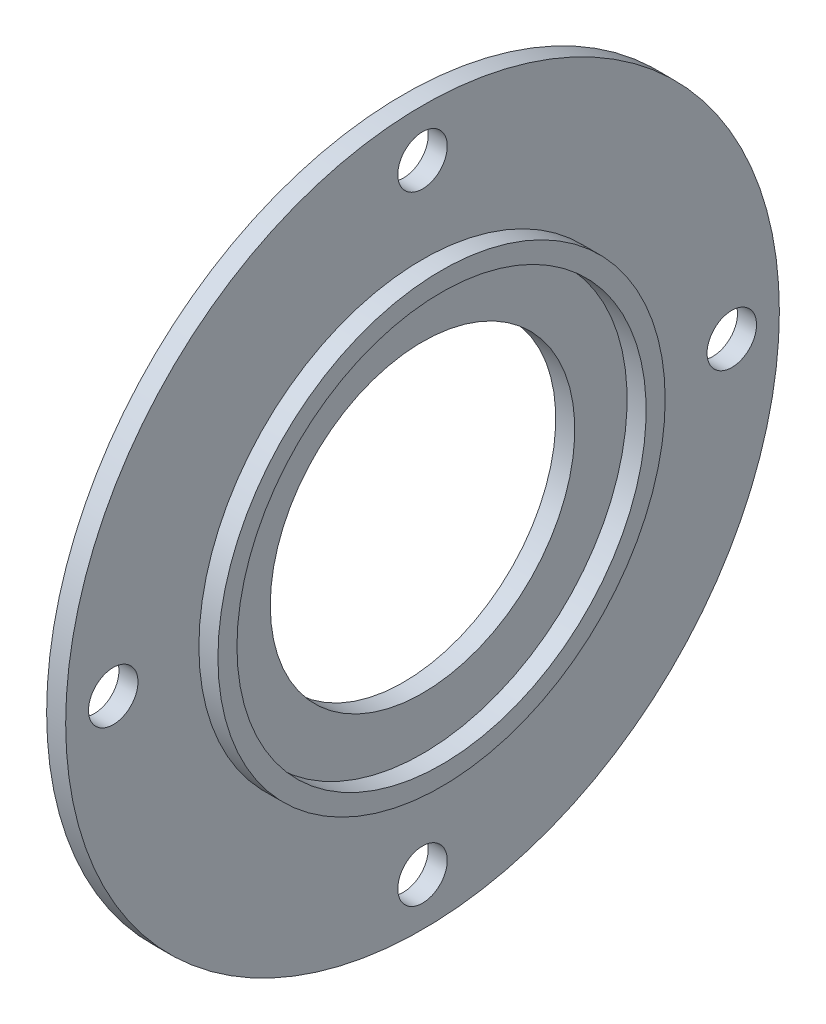
SolidWorks part; units mm, degrees
ref_plane "Ebene vorne" through (0, 0, 0) normal (0, 0, 1) x (1, 0, 0)
ref_plane "Ebene oben" through (0, 0, 0) normal (0, 1, 0) x (1, 0, 0)
ref_plane "Ebene rechts" through (0, 0, 0) normal (1, 0, 0) x (0, 0, -1)
sketch "Skizze1" plane through (0, 0, 0) normal (0, 0, 1) x (1, 0, 0)
  line L0 (0, 37.5) -> (0, 16)
  line L1 (4, 23.5) -> (2, 23.5)
  line L2 (4, 23.5) -> (4, 21.5)
  line L3 (4, 21.5) -> (2, 21.5)
  line L4 (2, 21.5) -> (2, 16)
  line L5 (-7.7434, 0) -> (14.5102, 0) construction
  line L6 (0, 16) -> (2, 16)
  line L7 (2, 23.5) -> (2, 37.5)
  line L8 (2, 37.5) -> (0, 37.5)
  dimension "D1" = 2
  dimension "D2" = 2
  dimension "D3" = 23.5
  dimension "D4" = 37.5
  dimension "D5" = 16
  dimension "D6" = 2
  dimension "D7" = 2
  dimension "D8" = 2
revolve "Rotation1" add sketch "Skizze1" angle 360 about L5
sketch "Skizze2" plane through (0, 0, 0) normal (-1, 0, 0) x (0, 0, 1)
  line L0 (0, 0) -> (0, 32.5)
  circle A0 centre (0, 0) radius 32.5
  dimension "D1" = 65
hole_wizard "Ø5.2 (5.2) Durchmesser Bohrung1" positions "Skizze6" profile "Skizze7" hole size "Ø5.2" standard "ANSI Metrisch"
sketch "Skizze6" plane through (0, 0, 0) normal (-1, 0, 0) x (0, 0, 1)
  point P0 (0, 32.5)
sketch "Skizze7" plane through (0, 32.5, 0) normal (0, 1, 0) x (0, 0, 1)
  line L0 (0, 0) -> (0, 31.5622)
  line L1 (0, 31.5622) -> (2.6, 30)
  line L2 (2.6, 30) -> (2.6, 0)
  line L5 (2.6, 0) -> (0, 0)
  line L10 (0, 31.5622) -> (-2.6, 30) construction
  line L11 (0, -6.35) -> (0, 107.95) construction
  dimension "Bohrerdurchmesser" = 5.2
  dimension "Bohrungstiefe" = 30
  dimension "Spitzenwinkel" = 118
pattern_circular "Kreismuster1" count 4 over 360 about axis through (0, 0, 0) along (1, 0, 0) of "Ø5.2 (5.2) Durchmesser Bohrung1"
